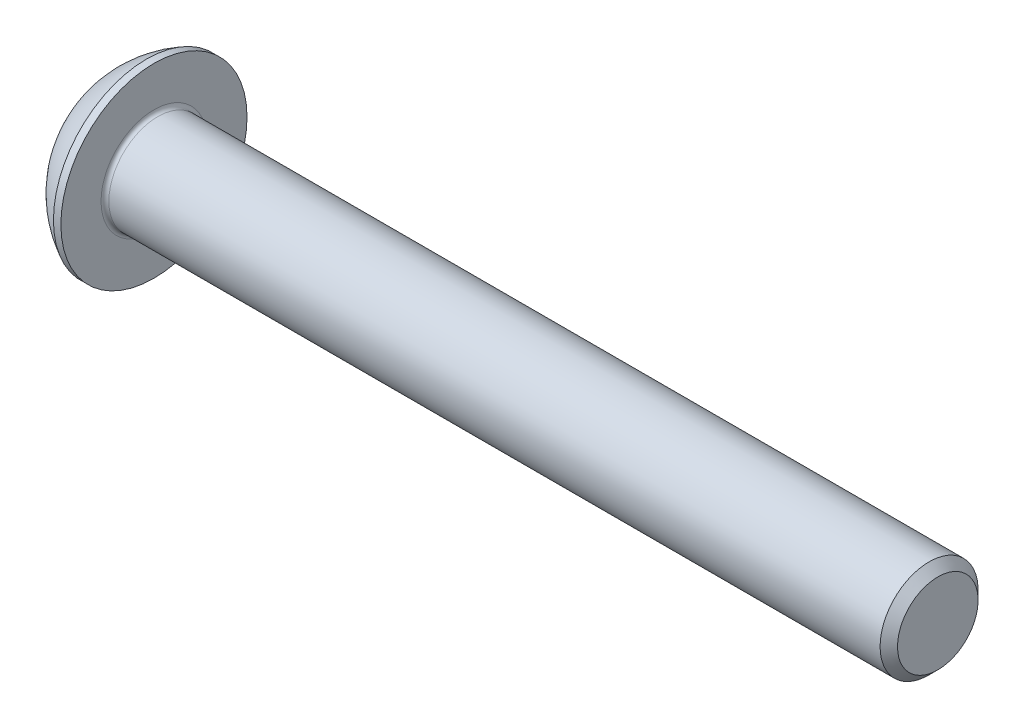
SolidWorks part; units mm, degrees
ref_plane "Plane1" through (0, 0, 0) normal (0, 0, 1) x (1, 0, 0)
ref_plane "Plane2" through (0, 0, 0) normal (0, 1, 0) x (1, 0, 0)
ref_plane "Plane3" through (0, 0, 0) normal (1, 0, 0) x (0, 0, -1)
sketch "BodySke" plane through (0, 0, 0) normal (0, 0, 1) x (1, 0, 0)
  line L0 (42.75, 0) -> (42.75, 2.055)
  line L1 (42.305, 2.5) -> (2.75, 2.5)
  line L2 (2.75, 2.5) -> (2.75, 4.75)
  line L3 (2.75, 4.75) -> (2.37, 4.75)
  line L4 (0, 0) -> (101.6, 0) construction
  line L5 (2.75, -4.75) -> (2.37, -4.75) construction
  line L6 (55.6768, -2.5) -> (2.75, -2.5) construction
  line L7 (42.75, 0) -> (0, 0)
  line L8 (0, 2.375) -> (0, -2.375) construction
  line L9 (0, 0) -> (0, 2.375)
  line L10 (42.75, 2.055) -> (42.305, 2.5)
  line L11 (42.75, -2.055) -> (42.305, -2.5) construction
  line L12 (3.55, 9.525) -> (3.55, -2.5) construction
  line L13 (2.75, 9.525) -> (2.75, -2.5) construction
  arc A1 (0, 2.375) -> (2.37, 4.75) centre (4.755, 0) cw
  dimension "Diameter" = 5
  dimension "Length" = 40
  dimension "Head_dia" = 9.5
  dimension "D1" = 4.75
  dimension "Head_ht" = 2.75
  dimension "Head_side_ht" = 0.38
  dimension "Minor_dia" = 4.11
  dimension "Body_ch_ang" = 45
  dimension "Advance" = 0.8
  dimension "Thread_nom" = 40
revolve "BaseBody" add sketch "BodySke" angle 360 about L4
cosmetic thread "ThreadCosmetic" [suppressed] parameters "Thread_length"=38.4, "Thread_minor"=4.11
fillet "Fillet1" radius 0.2 1 edges at (2.75, 0, 2.5)
sketch "Sketch2" plane through (0, 0, 0) normal (0, 0, 1) x (1, 0, 0)
  line L0 (0, 1.5) -> (1.56, 1.5)
  line L1 (1.56, 1.5) -> (2.426, 0)
  line L3 (2.426, 0) -> (0, 0)
  line L4 (0, 0) -> (0, 1.5)
  line L5 (0, -1.5) -> (1.56, -1.5) construction
  line L6 (0, 0) -> (47.625, 0) construction
  dimension "D2" = 60
  dimension "PreBroach_depth" = 1.56
  dimension "PreBroach_dia" = 3
revolve "PreBroach" cut sketch "Sketch2" angle 360 about L6
sketch "Sketch3" plane through (0, 0, 0) normal (1, 0, 0) x (0, 0, -1)
  line L0 (-1.5, -0.866) -> (-1.5, 0.866)
  line L1 (-1.5, 0.866) -> (0, 1.7321)
  line L2 (0, 1.7321) -> (1.5, 0.866)
  line L3 (1.5, 0.866) -> (1.5, -0.866)
  line L4 (1.5, -0.866) -> (0, -1.7321)
  line L5 (0, -1.7321) -> (-1.5, -0.866)
  dimension "Hex_size" = 3
  dimension "D3" = 3
  dimension "D1" = 1.5
  dimension "D2" = 1.5
extrude "Hex" cut sketch "Sketch3" along normal blind 1.56
sketch "ThdSchSke" plane through (0, 0, 0) normal (0, 0, 1) x (1, 0, 0)
  line L0 (4.35, -2.055) -> (4.0384, -2.5)
  line L1 (4.35, -2.055) -> (4.6616, -2.5)
  line L2 (4.6616, -2.5) -> (4.6616, -3.125)
  line L3 (-3.175, 0) -> (5.1513, 0) construction
  line L5 (4.6616, -3.125) -> (4.0384, -3.125)
  line L6 (4.0384, -3.125) -> (4.0384, -2.5)
  dimension "Diameter" = 5
  dimension "Thread_minor" = 4.11
  dimension "SideAngle" = 55
  dimension "VeeAngle" = 70
  dimension "Overcut" = 6.25
  dimension "Start" = 4.35
revolve "ThreadSchematic" [suppressed] cut sketch "ThdSchSke" angle 360 about L3
pattern_linear "ThdSchPat" [suppressed]
equation "\"D1@BodySke\" = \"Head_dia@BodySke\" * .5"
equation "\"Thread_minor@ThreadCosmetic\" = \"Minor_dia@BodySke\""
equation "\"D1@Sketch3\" = \"Hex_size@Sketch3\" / 2"
equation "\"D2@Sketch3\" = \"D1@Sketch3\""
equation "\"D3@Sketch3\" = \"Hex_size@Sketch3\""
equation "\"Thread_length@ThreadCosmetic\" = ((sgn( (\"Length@BodySke\" - \"Advance@BodySke\" * 2.0) - \"Thread_nom@BodySke\" )-1)*( (\"Length@BodySke\" - \"Advance@BodySke\" * 2.0) - \"Thread_nom@BodySke\" ))/-2+ \"Thread_nom@BodySke\""
equation "\"Thread_minor@ThdSchSke\" = \"Minor_dia@BodySke\""
equation "\"Diameter@ThdSchSke\" = \"Diameter@BodySke\""
equation "\"Overcut@ThdSchSke\" = \"Diameter@BodySke\" * 1.25"
equation "\"Start@ThdSchSke\" = \"Head_ht@BodySke\" + \"Length@BodySke\" - \"Thread_length@ThreadCosmetic\"  '---Non-countersunk---"
equation "\"Num_threads@ThdSchPat\" = int( \"Thread_length@ThreadCosmetic\" / \"Advance@BodySke\" + 0.999 )  + 1"
equation "\"Advance@ThdSchPat\" = \"Thread_length@ThreadCosmetic\" /  (\"Num_threads@ThdSchPat\" - 1) 'relax it"
equation "\"Num_threads@ThdSchPat\" = \"Num_threads@ThdSchPat\" - sgn( \"Num_threads@ThdSchPat\" - 1) '---chamfered tips only---"
